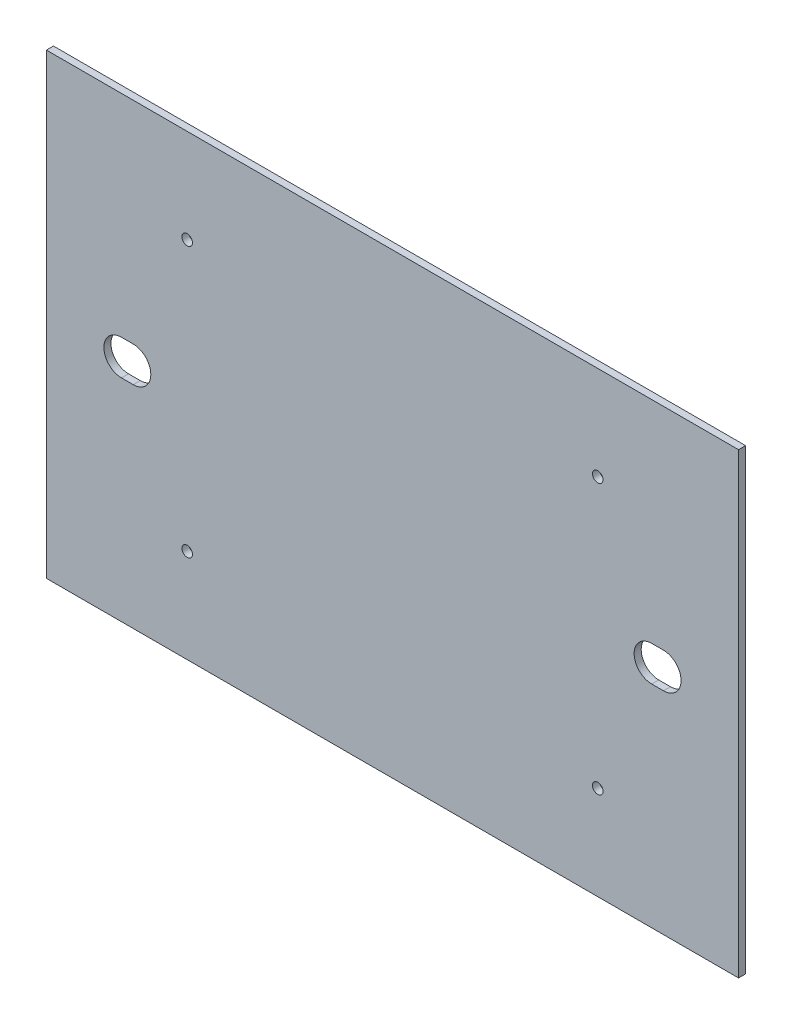
SolidWorks part; units mm, degrees
ref_plane "Plan de face" through (0, 0, 0) normal (0, 0, 1) x (1, 0, 0)
ref_plane "Plan de dessus" through (0, 0, 0) normal (0, 1, 0) x (1, 0, 0)
ref_plane "Plan de droite" through (0, 0, 0) normal (1, 0, 0) x (0, 0, -1)
sketch "Esquisse1" plane through (0, 0, 0) normal (0, 0, 1) x (1, 0, 0)
  line L0 (147.5, 0) -> (147.5, -195) construction
  line L1 (0, 0) -> (295, 0)
  line L2 (0, 0) -> (0, -195)
  line L3 (0, -195) -> (295, -195)
  line L4 (295, 0) -> (295, -195)
  line L5 (0, -97.5) -> (295, -97.5) construction
  line L6 (32, -74.163) -> (32, -119.0922) construction
  line L7 (258, -74.163) -> (258, -119.0922) construction
  line L8 (37, -74.163) -> (37, -119.0922) construction
  line L9 (32, -90) -> (37, -90)
  line L10 (32, -105) -> (37, -105)
  line L11 (263, -74.163) -> (263, -119.0922) construction
  line L12 (263, -105) -> (258, -105)
  line L13 (263, -90) -> (258, -90)
  circle A0 centre (60, -40) radius 2.25
  circle A1 centre (235, -40) radius 2.25
  circle A2 centre (235, -155) radius 2.25
  circle A3 centre (60, -155) radius 2.25
  arc A4 (32, -90) -> (32, -105) centre (32, -97.5) ccw
  arc A5 (258, -105) -> (258, -90) centre (258, -97.5) cw
  arc A6 (37, -105) -> (37, -90) centre (37, -97.5) ccw
  arc A7 (263, -90) -> (263, -105) centre (263, -97.5) cw
  dimension "D3" = 4.5
  dimension "D7" = 15
  dimension "D8" = 15
  dimension "D1" = 295
  dimension "D2" = 195
  dimension "D4" = 60
  dimension "D5" = 40
  dimension "D6" = 32
  dimension "D9" = 5
extrude "Boss.-Extru.1" add sketch "Esquisse1" along normal blind 3
